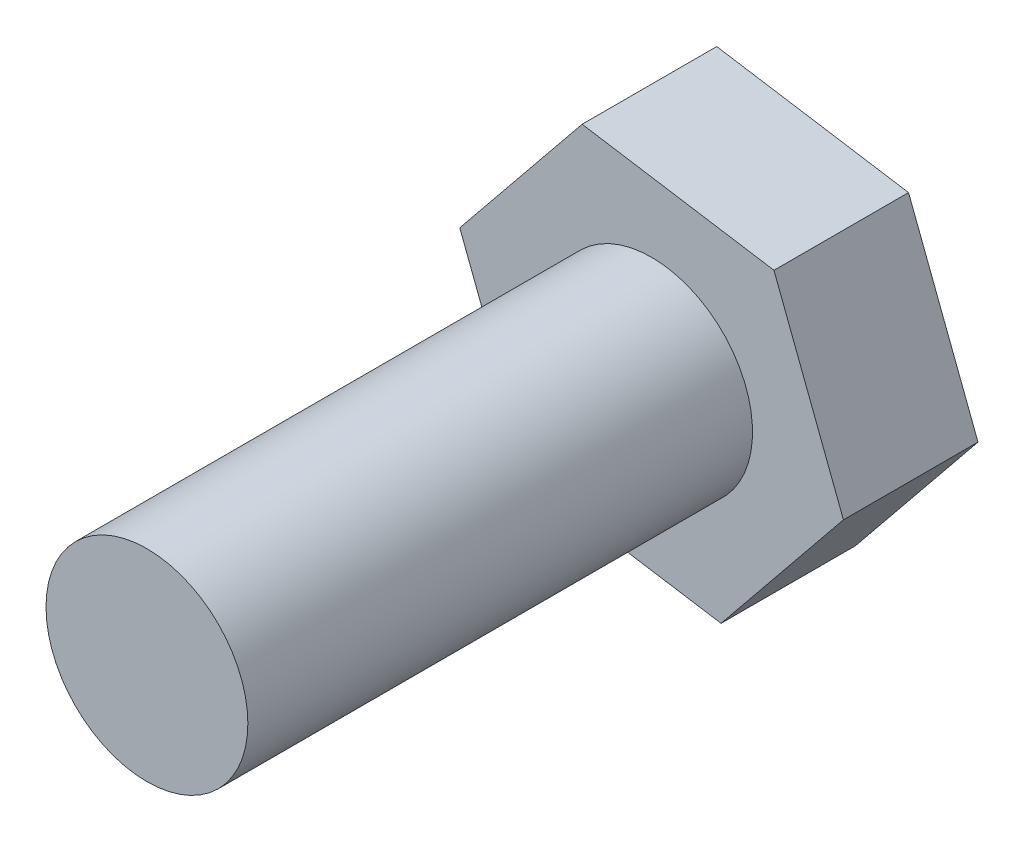
SolidWorks part; units mm, degrees
ref_plane "前视基准面" through (0, 0, 0) normal (0, 0, 1) x (1, 0, 0)
ref_plane "上视基准面" through (0, 0, 0) normal (0, 1, 0) x (1, 0, 0)
ref_plane "右视基准面" through (0, 0, 0) normal (1, 0, 0) x (0, 0, -1)
sketch "草图1" plane through (0, 0, 0) normal (0, 0, 1) x (1, 0, 0)
  circle A0 centre (0, 0) radius 0.3
extrude "凸台-拉伸1" add sketch "草图1" along normal blind 1.5
sketch "草图2" plane through (0, 0, 0) normal (0, 0, -1) x (-1, 0, 0)
  line L1 (0.3637, -0.4484) -> (0.5702, 0.0908)
  line L2 (0.5702, 0.0908) -> (0.2064, 0.5392)
  line L3 (0.2064, 0.5392) -> (-0.3637, 0.4484)
  line L4 (-0.3637, 0.4484) -> (-0.5702, -0.0908)
  line L5 (-0.5702, -0.0908) -> (-0.2064, -0.5392)
  line L6 (-0.2064, -0.5392) -> (0.3637, -0.4484)
  circle A0 centre (0, 0) radius 0.5 construction
  dimension "D1" = 1
extrude "凸台-拉伸2" add sketch "草图2" along normal blind 0.4
